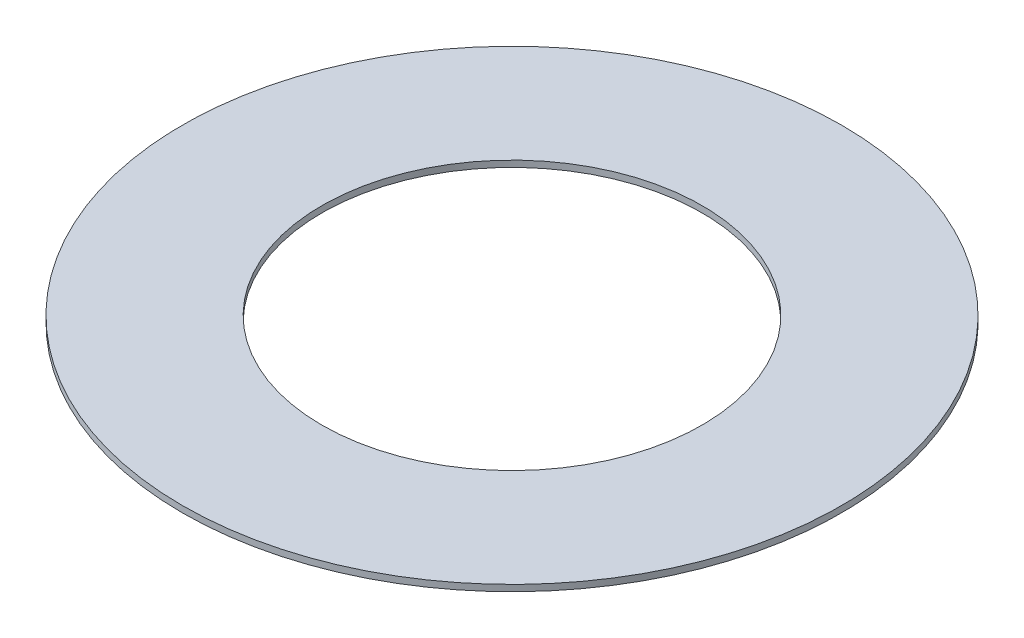
SolidWorks part; units mm, degrees
material "Thornel Mat VMA"
ref_plane "Front Plane" through (0, 0, 0) normal (0, 0, 1) x (1, 0, 0)
ref_plane "Top Plane" through (0, 0, 0) normal (0, 1, 0) x (1, 0, 0)
ref_plane "Right Plane" through (0, 0, 0) normal (1, 0, 0) x (0, 0, -1)
sketch "Sketch2" plane through (0, 0, 0) normal (0, 1, 0) x (1, 0, 0)
  circle A0 centre (0, 0) radius 66.04
  circle A1 centre (0, 0) radius 38.1
  dimension "D1" = 132.08
  dimension "D2" = 76.2
extrude "Boss-Extrude1" add sketch "Sketch2" along normal blind 1.27
